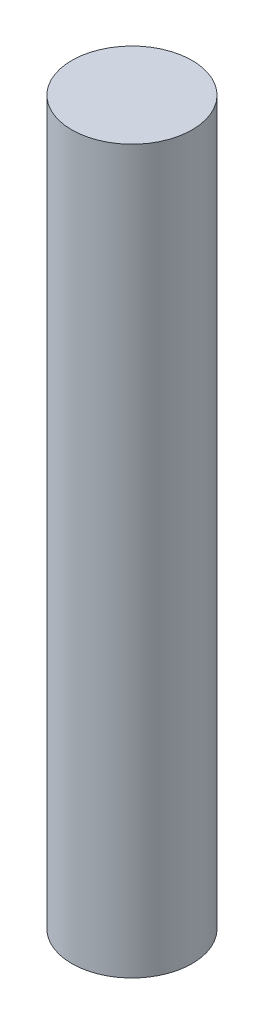
SolidWorks part; units mm, degrees
ref_plane "Front Plane" through (0, 0, 0) normal (0, 0, 1) x (1, 0, 0)
ref_plane "Top Plane" through (0, 0, 0) normal (0, 1, 0) x (1, 0, 0)
ref_plane "Right Plane" through (0, 0, 0) normal (1, 0, 0) x (0, 0, -1)
sketch "Sketch1" plane through (0, 0, 0) normal (0, 1, 0) x (1, 0, 0)
  circle A0 centre (0, 0) radius 1.875
  dimension "D1" = 3.75
extrude "Boss-Extrude1" add sketch "Sketch1" along normal blind 22.5
